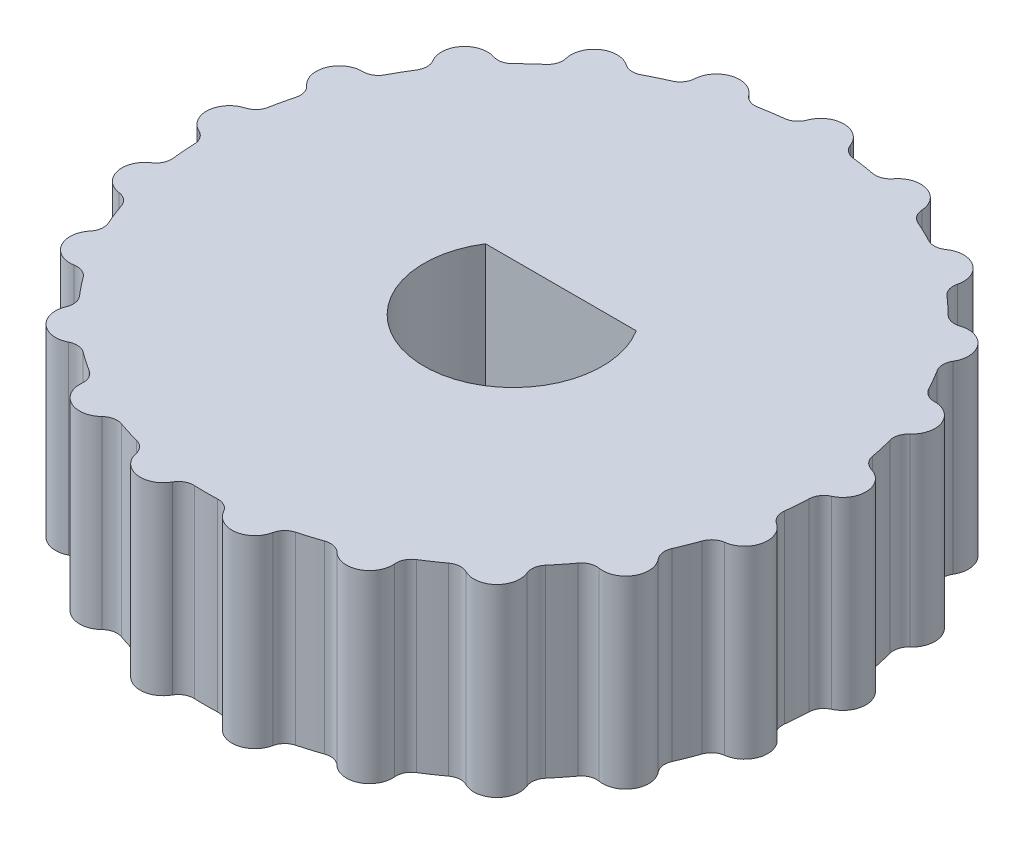
SolidWorks part; units mm, degrees
ref_plane "Front Plane" through (0, 0, 0) normal (0, 0, 1) x (1, 0, 0)
ref_plane "Top Plane" through (0, 0, 0) normal (0, 1, 0) x (1, 0, 0)
ref_plane "Right Plane" through (0, 0, 0) normal (1, 0, 0) x (0, 0, -1)
sketch "Sketch1" plane through (0, 0, 0) normal (0, 1, 0) x (1, 0, 0)
  line L0 (-2.451, 1.55) -> (2.451, 1.55)
  line L5 (0, 0) -> (10, 0) construction
  line L6 (0, 0) -> (0, -2.9) construction
  circle A0 centre (0, 0) radius 2.9
  circle A1 centre (0, 0) radius 10
  dimension "D1" = 5.8
  dimension "D2" = 20
  dimension "D3" = 4.45
extrude "Boss-Extrude1" add sketch "Sketch1" along normal blind 6 contours L0 A0 | A1 A0
sketch "Sketch2" plane through (0, 6, 0) normal (0, 1, 0) x (1, 0, 0)
  circle A0 centre (0, 10) radius 0.75
  circle A1 centre (0, 0) radius 10 construction
  dimension "D1" = 1.5
extrude "Boss-Extrude2" add sketch "Sketch2" against normal through all
fillet "Fillet1" radius 0.5 2 edges at (0.7495, 3, -9.9719) (-0.7495, 3, -9.9719)
pattern_circular "CirPattern1" count 21 over 360 about axis through (0, 0, 0) along (0, 1, 0) of "Boss-Extrude2", "Fillet1"
